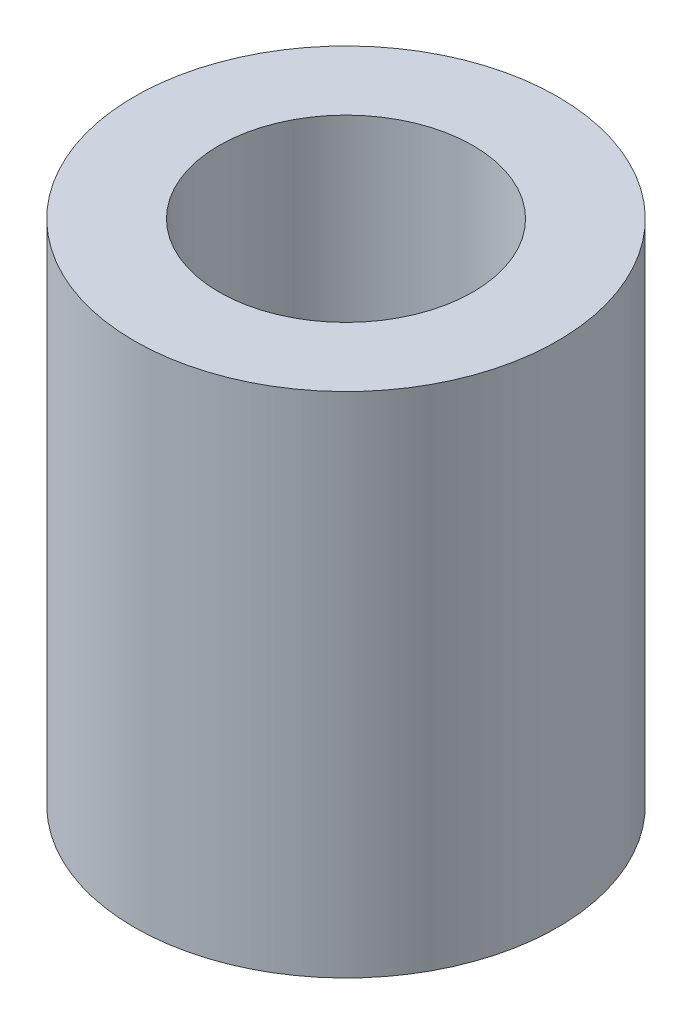
SolidWorks part; units mm, degrees
ref_plane "Front Plane" through (0, 0, 0) normal (0, 0, 1) x (1, 0, 0)
ref_plane "Top Plane" through (0, 0, 0) normal (0, 1, 0) x (1, 0, 0)
ref_plane "Right Plane" through (0, 0, 0) normal (1, 0, 0) x (0, 0, -1)
sketch "Sketch1" plane through (0, 0, 0) normal (0, 1, 0) x (1, 0, 0)
  circle A0 centre (0, 0) radius 5
  circle A1 centre (0, 0) radius 3
  dimension "D1" = 10
  dimension "D2" = 6
extrude "Boss-Extrude1" add sketch "Sketch1" along normal blind 12
